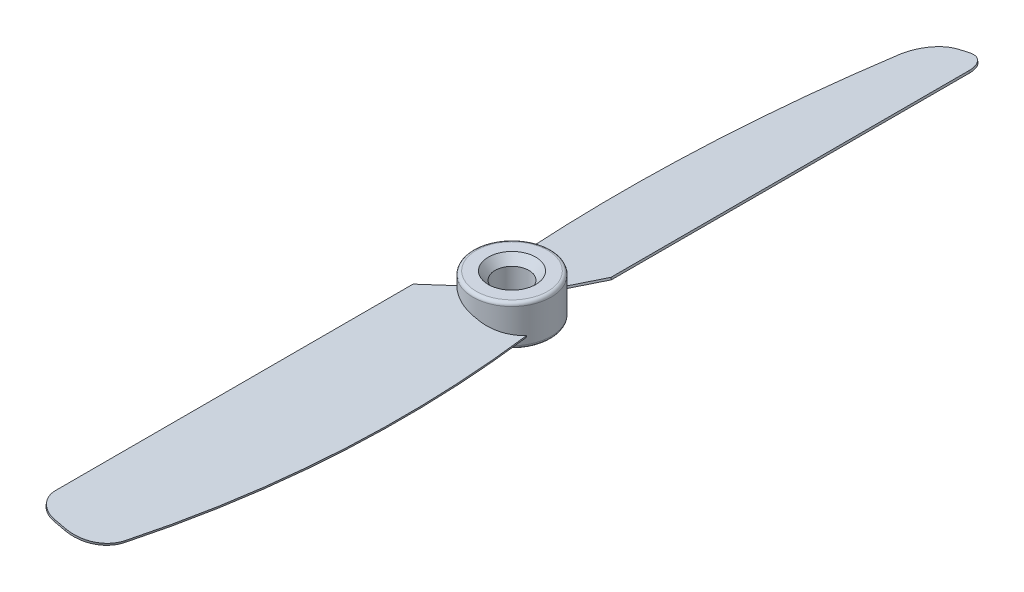
SolidWorks part; units mm, degrees
ref_plane "Front Plane" through (0, 0, 0) normal (0, 0, 1) x (1, 0, 0)
ref_plane "Top Plane" through (0, 0, 0) normal (0, 1, 0) x (1, 0, 0)
ref_plane "Right Plane" through (0, 0, 0) normal (1, 0, 0) x (0, 0, -1)
sketch "Sketch1" plane through (0, 0, 0) normal (0, 1, 0) x (1, 0, 0)
  circle A0 centre (0, 0) radius 5.75
  dimension "D1" = 11.5
extrude "Boss-Extrude1" add sketch "Sketch1" along normal mid plane 6
sketch "Sketch2" plane through (0, 0, 0) normal (0, 0, 1) x (1, 0, 0)
  line L0 (-5.75, 1.3275) -> (5.75, -1.3275) construction
  line L1 (-5.75, 3) -> (-5.75, -3) construction
  line L2 (5.75, -3) -> (5.75, 3) construction
  line L3 (-5.75, -3) -> (5.75, -3) construction
  dimension "D1" = 13
ref_plane "Plane1" through (0, 0, 0) normal (-0.225, -0.9744, 0) x (0.9744, -0.225, 0)
sketch "Sketch3" plane through (0, 0, 0) normal (-0.225, -0.9744, 0) x (0.9744, -0.225, 0)
  line L0 (-3.781, 3.4856) -> (-7.0738, 7.725)
  line L1 (-7.0738, 7.725) -> (-7.0738, 60.5)
  line L2 (-4.0738, 63.5) -> (-2.3608, 63.5)
  arc A0 (2.5299, 59.5396) -> (-2.3608, 63.5) centre (-2.3608, 58.5) ccw
  arc A1 (-7.0738, 60.5) -> (-4.0738, 63.5) centre (-4.0738, 60.5) cw
  ellipse E0 centre (0.6749, 0) end of major axis (0.6749, 5.75) minor radius 5.6026 construction
  ellipse E1 centre (0.6749, 0) end of major axis (0.6749, 5.75) minor radius 5.6026 (5.3794, 3.1225) -> (-3.781, 3.4856) ccw
  spline S0 degree 3 poles (5.3794, 3.1225) (7.4239, 22.1537) (6.4579, 41.0615) (2.5299, 59.5396) knots 0 0 0 0 0.933242 0.933242 0.933242 0.933242
  dimension "D2" = 5
  dimension "D3" = 3
  dimension "D1" = 63.5
extrude "Boss-Extrude2" add sketch "Sketch3" along normal mid plane 0.3
pattern_circular "CirPattern1" count 2 over 360 about axis through (0, 3, 0) along (0, -1, 0) of "Boss-Extrude2"
sketch "Sketch4" plane through (0, 3, 0) normal (0, 1, 0) x (1, 0, 0)
  circle A0 centre (0, 0) radius 2.5
  dimension "D1" = 5
extrude "Cut-Extrude1" cut sketch "Sketch4" against normal through all
fillet "Fillet1" radius 0.5 2 edges at (0, -3, 5.75) (0, 3, 5.75)
chamfer "Chamfer1" distance 1 angle 50 2 edges at (0, 3, 2.5) (0, -3, 2.5)
